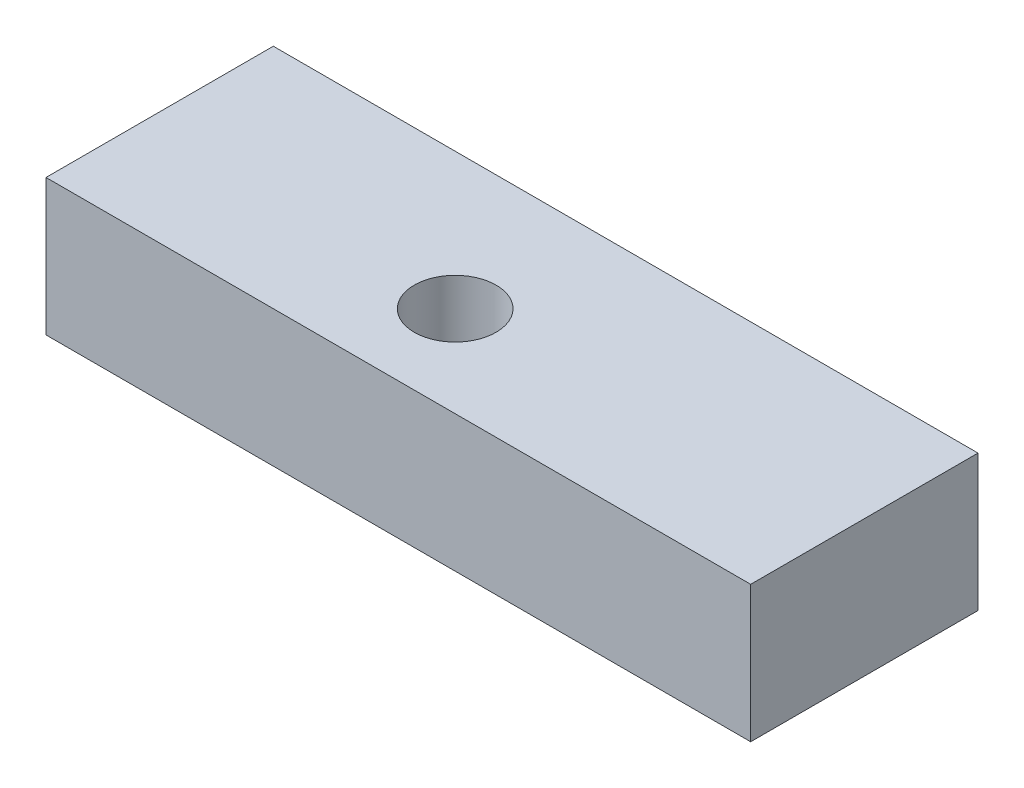
SolidWorks part; units mm, degrees
ref_plane "Front" through (0, 0, 0) normal (0, 0, 1) x (1, 0, 0)
ref_plane "Top" through (0, 0, 0) normal (0, 1, 0) x (1, 0, 0)
ref_plane "Right" through (0, 0, 0) normal (1, 0, 0) x (0, 0, -1)
sketch "Sketch1" plane through (0, 0, 0) normal (0, 1, 0) x (1, 0, 0)
  line L1 (-70, 30) -> (85, 30)
  line L2 (-70, 30) -> (-70, -20)
  line L3 (-70, -20) -> (85, -20)
  line L4 (85, 30) -> (85, -20)
  circle A0 centre (0, 0) radius 9
  dimension "D1" = 18
  dimension "D2" = 50
  dimension "D3" = 155
  dimension "D4" = 70
  dimension "D5" = 30
extrude "Boss-Extrude1" add sketch "Sketch1" along normal blind 30
equation "\"Length\" = 155mm'Match working Model"
equation "\"D3@Sketch1\"= \"Length\""
equation "\"ΔTCPC\"= 30mm'Between 0-5cm (Working Models should have minimum of 2cm already to reach the 2-7cm ΔTCPC specifications )in 0.5cm increments"
equation "\"D1@Boss-Extrude1\" = \"ΔTCPC\""
equation "\"Width\"= 50.00mm'Match working Model"
equation "\"D2@Sketch1\"=\"Width\""
